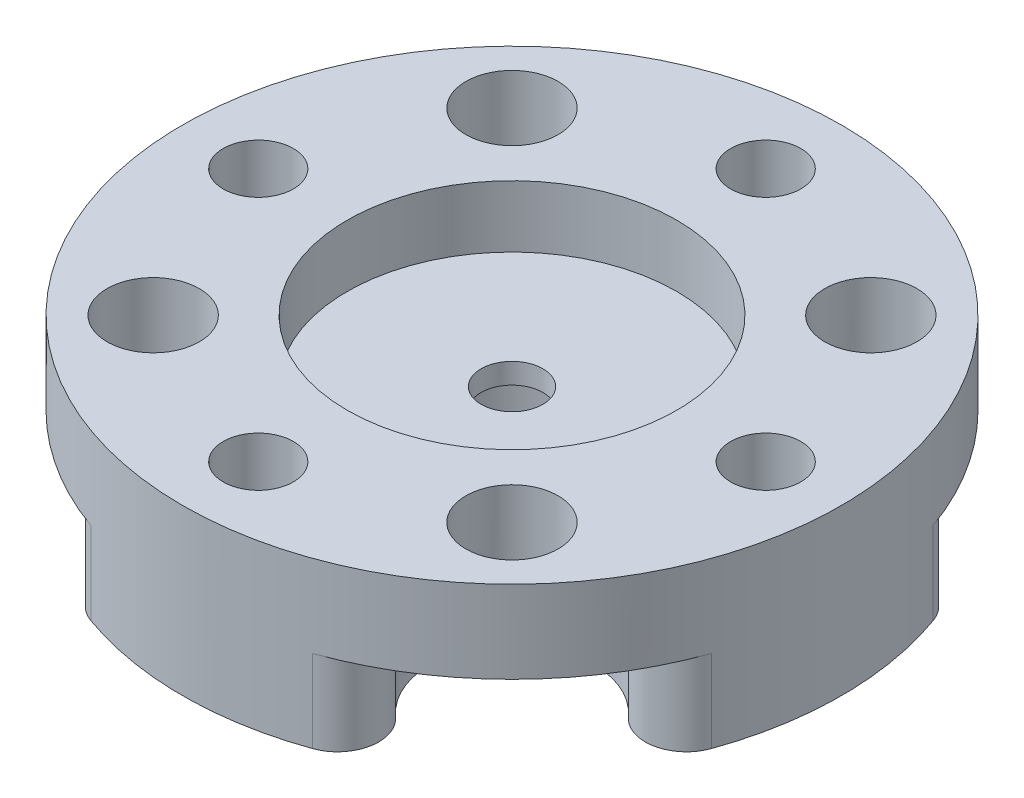
SolidWorks part; units mm, degrees
ref_plane "Front Plane" through (0, 0, 0) normal (0, 0, 1) x (1, 0, 0)
ref_plane "Top Plane" through (0, 0, 0) normal (0, 1, 0) x (1, 0, 0)
ref_plane "Right Plane" through (0, 0, 0) normal (1, 0, 0) x (0, 0, -1)
sketch "Sketch1" plane through (0, 0, 0) normal (0, 1, 0) x (1, 0, 0)
  circle A0 centre (0, 0) radius 12.7
  dimension "D1" = 25.4
extrude "Boss-Extrude1" add sketch "Sketch1" along normal blind 6.35
sketch "Sketch2" plane through (0, 6.35, 0) normal (0, 1, 0) x (1, 0, 0)
  circle A0 centre (0, 0) radius 6.35
  dimension "D1" = 12.7
extrude "Cut-Extrude1" cut sketch "Sketch2" against normal blind 2.3813
sketch "Sketch3" plane through (0, 0, 0) normal (0, -1, 0) x (1, 0, 0)
  circle A0 centre (0, 0) radius 3.1115
  dimension "D1" = 6.223
extrude "Cut-Extrude2" cut sketch "Sketch3" against normal blind 3.175
sketch "Sketch4" plane through (0, 3.9688, 0) normal (0, 1, 0) x (1, 0, 0)
  circle A0 centre (0, 0) radius 1.1906
  dimension "D1" = 2.3813
extrude "Cut-Extrude3" cut sketch "Sketch4" against normal through all
hole_wizard "#6-32 Tapped Hole1" positions "Sketch6" profile "Sketch5" tap size "#6-32" standard "ANSI Inch" end condition through all
sketch "Sketch6" plane through (0, 6.35, 0) normal (0, 1, 0) x (1, 0, 0)
  point P2 (-9.779, 0)
sketch "Sketch5" plane through (-9.779, 6.35, 0) normal (1, 0, 0) x (0, 0, 1)
  line L0 (0, 0) -> (0, 6.35)
  line L1 (0, 6.35) -> (1.3525, 6.35)
  line L2 (1.3525, 6.35) -> (1.3525, 0)
  line L5 (1.3525, 0) -> (0, 0)
  line L11 (0, -6.35) -> (0, 107.95) construction
  dimension "Thru Tap Drill Dia." = 2.7051
  dimension "Thru Tap Drill Depth" = 6.35
cosmetic thread "Hole Thread5" parameters "D2"=3.5052
sketch "Sketch7" plane through (0, 6.35, 0) normal (0, 1, 0) x (1, 0, 0)
  line L0 (0, 0) -> (6.9148, -6.9148) construction
  line L1 (0, 0) -> (0, -14.541) construction
  circle A0 centre (6.9148, -6.9148) radius 1.778
  dimension "D3" = 3.556
  dimension "D1" = 45
  dimension "D2" = 9.779
extrude "Cut-Extrude4" cut sketch "Sketch7" against normal through all
sketch "Sketch8" plane through (0, 0, 0) normal (0, -1, 0) x (1, 0, 0)
  circle A0 centre (6.9148, 6.9148) radius 3.175
  dimension "D1" = 6.35
extrude "Cut-Extrude5" cut sketch "Sketch8" against normal blind 3.175
pattern_circular "CirPattern2" count 4 over 360 about axis through (0, 0, 0) along (0, 1, 0) of "#6-32 Tapped Hole1", "Cut-Extrude4", "Cut-Extrude5"
fillet "Fillet1" radius 1.5875 8 edges at (7.9231, 1.5875, 9.9254) (9.9254, 1.5875, 7.9231) (9.9254, 1.5875, -7.9231) (7.9231, 1.5875, -9.9254) (-7.9231, 1.5875, -9.9254) (-9.9254, 1.5875, -7.9231) (-9.9254, 1.5875, 7.9231) (-7.9231, 1.5875, 9.9254)
sketch "Angle line" plane through (0, 6.35, 0) normal (0, 1, 0) x (1, 0, 0)
  line L0 (0, -9.779) -> (0, 9.779) construction
